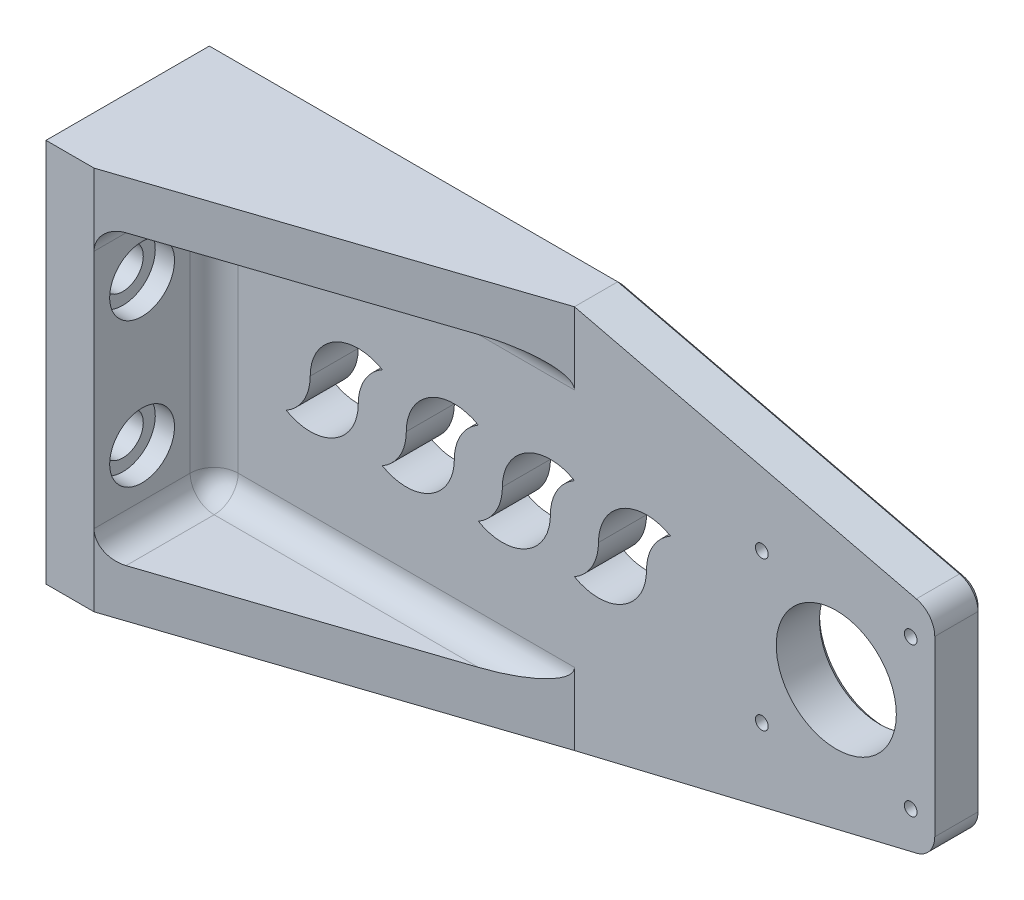
SolidWorks part; units mm, degrees
ref_plane "Front Plane" through (0, 0, 0) normal (0, 0, 1) x (1, 0, 0)
ref_plane "Top Plane" through (0, 0, 0) normal (0, 1, 0) x (1, 0, 0)
ref_plane "Right Plane" through (0, 0, 0) normal (1, 0, 0) x (0, 0, -1)
sketch "Sketch1" plane through (0, 0, 0) normal (0, 0, 1) x (1, 0, 0)
  line L1 (-80, -40) -> (80, -40)
  line L2 (-80, -40) -> (-80, 40)
  line L3 (-80, 40) -> (80, 40)
  line L4 (80, -40) -> (80, 40)
  line L5 (-80, -40) -> (80, 40) construction
  line L6 (-80, 40) -> (80, -40) construction
  point P0 (0, 0)
  dimension "D1" = 160
  dimension "D2" = 80
extrude "Boss-Extrude1" add sketch "Sketch1" along normal blind 10
sketch "Sketch2" plane through (0, 0, 10) normal (0, 0, 1) x (1, 0, 0)
  line L0 (0, 0) -> (59.5, 0) construction
  line L1 (44, -15.5) -> (75, -15.5) construction
  line L2 (44, -15.5) -> (44, 15.5) construction
  line L3 (44, 15.5) -> (75, 15.5) construction
  line L4 (75, -15.5) -> (75, 15.5) construction
  line L5 (44, -15.5) -> (75, 15.5) construction
  line L6 (44, 15.5) -> (75, -15.5) construction
  line L7 (80, -40) -> (80, 40) construction
  circle A0 centre (44, 15.5) radius 1.325
  circle A1 centre (75, 15.5) radius 1.325
  circle A2 centre (44, -15.5) radius 1.325
  circle A3 centre (75, -15.5) radius 1.325
  circle A4 centre (59.5, 0) radius 12.5
  point P0 (59.5, 0)
  dimension "D4" = 2.65
  dimension "D5" = 25
  dimension "D1" = 31
  dimension "D2" = 31
  dimension "D3" = 5
sketch "Sketch3" plane through (0, 0, 10) normal (0, 0, 1) x (1, 0, 0)
extrude "Cut-Extrude1" cut sketch "Sketch2" against normal blind 3
sketch "Sketch4" plane through (0, 0, 7) normal (0, 0, 1) x (1, 0, 0)
  circle A0 centre (75, -15.5) radius 1.325 construction
  circle A1 centre (44, -15.5) radius 1.325 construction
  circle A2 centre (75, 15.5) radius 1.325 construction
  circle A3 centre (44, 15.5) radius 1.325 construction
  circle A4 centre (75, -15.5) radius 1.325
  circle A5 centre (44, -15.5) radius 1.325
  circle A6 centre (75, 15.5) radius 1.325
  circle A7 centre (44, 15.5) radius 1.325
  circle A8 centre (59.5, 0) radius 12.5
  dimension "D1" = 25
extrude "Cut-Extrude2" cut sketch "Sketch4" against normal up to next
sketch "Sketch7" plane through (0, 0, 10) normal (0, 0, 1) x (1, 0, 0)
  line L0 (-80, -40) -> (80, -40) construction
  line L1 (-80, 40) -> (-70, 40)
  line L2 (-80, 40) -> (-80, -40)
  line L3 (-80, -40) -> (-70, -40)
  line L4 (-70, 40) -> (-70, -40)
  dimension "D1" = 10
extrude "Boss-Extrude3" add sketch "Sketch7" along normal blind 25
sketch "Sketch8" plane through (0, 40, 0) normal (0, 1, 0) x (1, 0, 0)
  line L0 (-70, -35) -> (5, -10)
  line L1 (80, -10) -> (-70, -10) construction
  line L2 (5, -10) -> (-70, -10)
  line L3 (-70, -10) -> (-70, -35)
extrude "Boss-Extrude4" add sketch "Sketch8" against normal blind 10
sketch "Sketch9" plane through (0, -40, 0) normal (0, -1, 0) x (1, 0, 0)
  line L3 (-70, 35) -> (-70, 10)
  line L4 (-70, 10) -> (5, 10)
  line L5 (5, 10) -> (-70, 35)
  line L6 (-70, 35) -> (-70, 10)
  line L7 (-70, 10) -> (5, 10)
  line L8 (5, 10) -> (-70, 35)
  dimension "D1" = 0
extrude "Boss-Extrude5" add sketch "Sketch9" against normal blind 10
sketch "Sketch10" plane through (0, 0, 10) normal (0, 0, 1) x (1, 0, 0)
  circle A0 centre (0, 0) radius 10
  circle A1 centre (-10, 0) radius 10
  circle A2 centre (-20, 0) radius 10
  circle A3 centre (-30, 0) radius 10
  circle A4 centre (-40, 0) radius 10
  circle A5 centre (-50, 0) radius 10
  circle A6 centre (-60, 0) radius 10
  circle A7 centre (10, 0) radius 10
  circle A8 centre (20, 0) radius 10
  circle A9 centre (30, 0) radius 10
  dimension "D1" = 20
extrude "Cut-Extrude3" cut sketch "Sketch10" against normal up to next contours A6 A5 A4 | A5 A4 | A5 A3 A4 | A4 A3 A2 | A3 A2 | A3 A1 A2 | A2 A1 A0 | A0 A1 | A7 A0 A1 | A8 A0 A7 | A7 A8 | A9 A8 A7
sketch "Sketch11" plane through (0, 0, 10) normal (0, 0, 1) x (1, 0, 0)
  line L0 (80, 22) -> (5, 40)
  line L1 (80, -40) -> (80, 40) construction
  line L2 (5, 40) -> (80, 40)
  line L3 (80, 40) -> (80, 22)
  line L4 (-80, 0) -> (80, 0) construction
  line L5 (-80, 40) -> (-80, -40) construction
  line L6 (80, -40) -> (80, -22)
  line L7 (5, -40) -> (80, -40)
  line L8 (80, -22) -> (5, -40)
  dimension "D1" = 18
extrude "Cut-Extrude4" cut sketch "Sketch11" against normal blind 10
fillet "Fillet1" radius 5 5 edges at (-32.5, -30, 10) (-70, -30, 22.5) (-70, 0, 10) (-70, 30, 22.5) (-32.5, 30, 10)
sketch "Sketch12" plane through (0, 0, 0) normal (0, 0, -1) x (-1, 0, 0)
  circle A0 centre (-75, 15.5) radius 3.25
  circle A1 centre (-44, 15.5) radius 3.25
  circle A2 centre (-44, -15.5) radius 3.25
  circle A3 centre (-75, -15.5) radius 3.25
  dimension "D1" = 6.5
extrude "Cut-Extrude5" cut sketch "Sketch12" against normal blind 4.5
sketch "Sketch13" plane through (-70, 0, 0) normal (1, 0, 0) x (0, 0, -1)
  line L0 (-25, -25) -> (-25, 25) construction
  line L1 (-35, -25) -> (-15, -25) construction
  line L2 (-15, 25) -> (-35, 25) construction
  line L3 (-35, 0) -> (-15, 0) construction
  line L4 (-35, -25) -> (-35, 25) construction
  line L5 (-15, -25) -> (-15, 25) construction
  circle A0 centre (-25, 15) radius 4.25
  circle A1 centre (-25, -15) radius 4.25
  dimension "D2" = 8.5
  dimension "D1" = 15
extrude "Cut-Extrude6" cut sketch "Sketch13" against normal up to next
sketch "Sketch14" plane through (-70, 0, 0) normal (1, 0, 0) x (0, 0, -1)
  circle A0 centre (-25, 15) radius 6.75
  circle A1 centre (-25, -15) radius 6.75
  dimension "D1" = 13.5
extrude "Cut-Extrude7" cut sketch "Sketch14" against normal blind 4
fillet "Fillet2" radius 5 2 edges at (80, -22, 5) (80, 22, 5)
chamfer "Chamfer2" distance 1 angle 45 9 edges at (47, 0, 0) (78.9265, 21.1536, 0) (40.5834, 31.46, 0) (-37.5, 40, 0) (-80, 0, 0) (-37.5, -40, 0) (40.5834, -31.46, 0) (78.9265, -21.1536, 0) (80, 0, 0)
